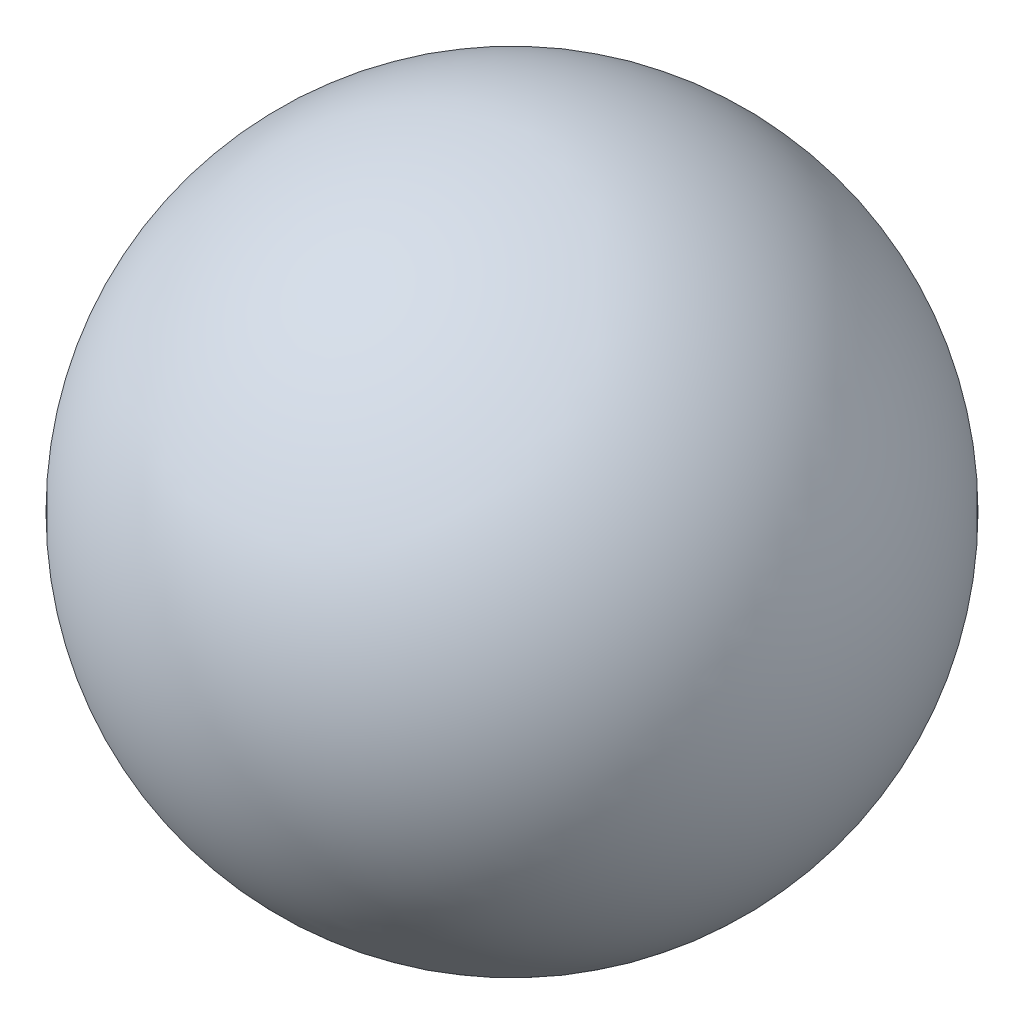
SolidWorks part; units mm, degrees
material "Polyurethane Foam Flexible"
ref_plane "Front Plane" through (0, 0, 0) normal (0, 0, 1) x (1, 0, 0)
ref_plane "Top Plane" through (0, 0, 0) normal (0, 1, 0) x (1, 0, 0)
ref_plane "Right Plane" through (0, 0, 0) normal (1, 0, 0) x (0, 0, -1)
sketch "Sketch1" plane through (0, 0, 0) normal (0, 1, 0) x (1, 0, 0)
  line L0 (0, 0) -> (15.0868, 15.0868)
  line L1 (0, 0) -> (-15.0868, -15.0868)
  arc A0 (-15.0868, -15.0868) -> (15.0868, 15.0868) centre (0, 0) ccw
  dimension "D1" = 42.672
revolve "Revolve1" add sketch "Sketch1" angle 360 about L0
